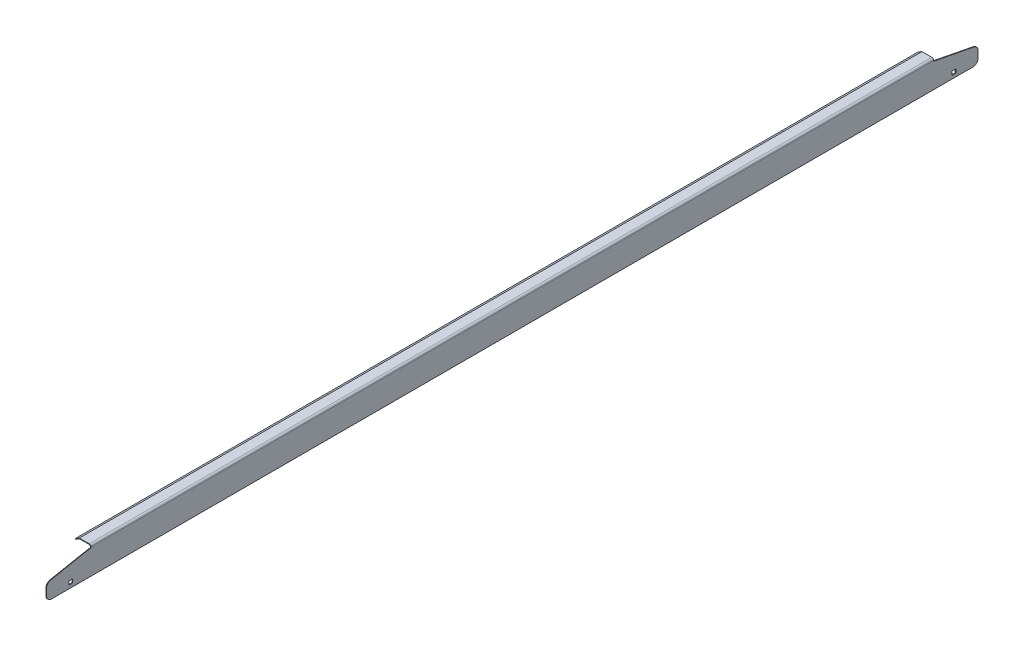
SolidWorks part; units mm, degrees
ref_plane "Front Plane" through (0, 0, 0) normal (0, 0, 1) x (1, 0, 0)
ref_plane "Top Plane" through (0, 0, 0) normal (0, 1, 0) x (1, 0, 0)
ref_plane "Right Plane" through (0, 0, 0) normal (1, 0, 0) x (0, 0, -1)
sketch "Sketch1" plane through (0, 0, 0) normal (0, 0, 1) x (1, 0, 0)
  line L0 (1143, 0) -> (1142.2062, 0)
  line L1 (1143, 32.5437) -> (1143, 0)
  line L2 (1142.2062, 0) -> (1142.2062, 32.5437)
  line L3 (1127.9187, 34.925) -> (1140.6188, 34.925)
  line L4 (1140.6188, 34.1313) -> (1128.1405, 34.1313)
  line L5 (1123.0914, 31.0712) -> (1128.1405, 34.1313)
  line L6 (1122.68, 31.75) -> (1123.0914, 31.0712)
  line L7 (1127.9187, 34.925) -> (1122.68, 31.75)
  arc A0 (1143, 32.5437) -> (1140.6188, 34.925) centre (1140.6188, 32.5437) ccw
  arc A1 (1142.2062, 32.5437) -> (1140.6188, 34.1313) centre (1140.6188, 32.5437) ccw
extrude "Extrude1" add sketch "Sketch1" along normal mid plane 1198.5625
sketch "Sketch2" plane through (1143, 0, 0) normal (1, 0, 0) x (0, 0, -1)
  line L0 (599.2812, 0) -> (599.2812, 20.6502) construction
  line L1 (599.2812, 0) -> (599.2812, 32.5437) construction
  line L2 (599.2812, 34.925) -> (542.1313, 34.925)
  line L3 (-599.2812, 34.925) -> (599.2812, 34.925) construction
  line L4 (542.1313, 34.925) -> (542.1312, 31.75)
  line L5 (542.1312, 31.75) -> (599.2812, 20.6502)
  line L6 (599.2812, 20.6502) -> (599.2812, 34.925)
  line L7 (-599.2812, 0) -> (-599.2812, 20.6502) construction
  line L8 (-599.2812, 0) -> (-599.2812, 32.5437) construction
  line L9 (-599.2812, 34.925) -> (-542.1312, 34.925)
  line L10 (-542.1312, 34.925) -> (-542.1312, 31.75)
  line L11 (-542.1312, 31.75) -> (-599.2812, 20.6502)
  line L12 (-599.2812, 20.6502) -> (-599.2812, 34.925)
extrude "Cut-Extrude1" cut sketch "Sketch2" against normal blind 25.4
sketch "Sketch3" plane through (0, 0, -542.1312) normal (0, 0, -1) x (-1, 0, 0)
  line L0 (-1127.9187, 34.925) -> (-1122.68, 31.75)
  line L1 (-1122.68, 31.75) -> (-1123.4204, 30.5283)
  line L2 (-1123.4204, 30.5283) -> (-1128.1405, 34.1313)
  line L3 (-1128.1405, 34.1313) -> (-1127.9187, 34.925)
extrude "Cut-Extrude2" cut sketch "Sketch3" along normal blind 25.4
sketch "Sketch4" plane through (0, 0, 542.1312) normal (0, 0, 1) x (1, 0, 0)
  line L0 (1127.9187, 34.925) -> (1122.68, 31.75)
  line L1 (1122.68, 31.75) -> (1124.0006, 29.571)
  line L2 (1124.0006, 29.571) -> (1128.1405, 34.1313)
  line L3 (1128.1405, 34.1313) -> (1127.9187, 34.925)
extrude "Cut-Extrude3" cut sketch "Sketch4" along normal blind 25.4
sketch "Sketch5" plane through (1143, 0, 0) normal (1, 0, 0) x (0, 0, -1)
  line L0 (599.2812, 0) -> (570.7062, 0) construction
  line L1 (-599.2812, 0) -> (599.2812, 0) construction
  line L2 (570.7062, 0) -> (570.7062, 4.2418) construction
  line L3 (-599.2812, 0) -> (-570.7062, 0) construction
  line L4 (570.7062, 4.2418) -> (565.9438, 4.2418)
  line L5 (570.7062, 4.2418) -> (570.7062, 9.0043)
  line L6 (570.7062, 9.0043) -> (565.9438, 9.0043)
  line L7 (565.9438, 4.2418) -> (565.9438, 9.0043)
  line L8 (-570.7062, 0) -> (-570.7062, 4.2418) construction
  line L10 (-570.7062, 4.2418) -> (-565.9438, 4.2418)
  line L11 (-570.7062, 4.2418) -> (-570.7062, 9.0043)
  line L12 (-570.7062, 9.0043) -> (-565.9438, 9.0043)
  line L13 (-565.9438, 4.2418) -> (-565.9438, 9.0043)
extrude "Cut-Extrude4" cut sketch "Sketch5" against normal up to surface (0.7938 mm away) up to face at (1142.2062, 21.236, 0)
fillet "Fillet1" radius 6.35 4 edges at (1142.6031, 0, 599.2812) (1142.6031, 20.6502, 599.2812) (1142.6031, 0, -599.2812) (1142.6031, 20.6502, -599.2812)
